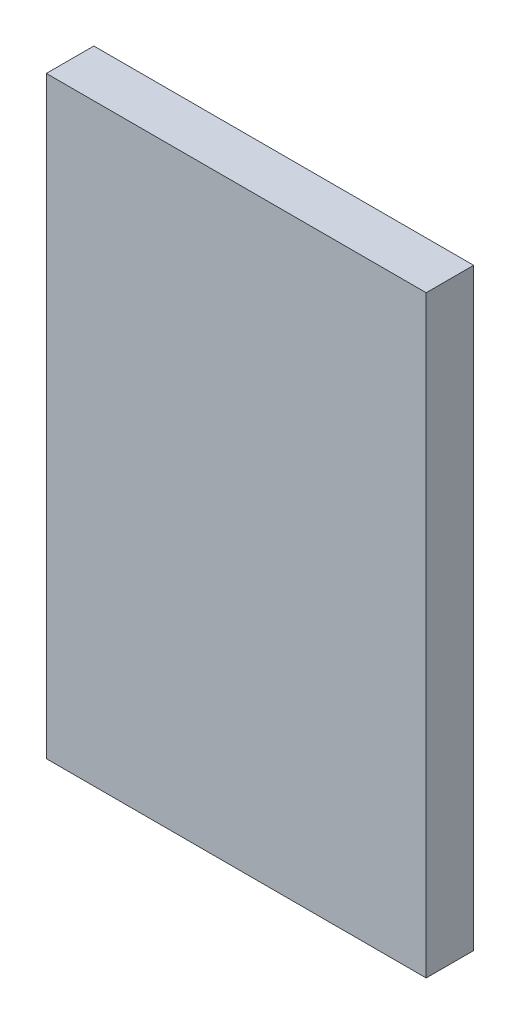
SolidWorks part; units mm, degrees
ref_plane "Alzado" through (0, 0, 0) normal (0, 0, 1) x (1, 0, 0)
ref_plane "Planta" through (0, 0, 0) normal (0, 1, 0) x (1, 0, 0)
ref_plane "Vista lateral" through (0, 0, 0) normal (1, 0, 0) x (0, 0, -1)
sketch "Croquis1" plane through (0, 0, 0) normal (0, 0, 1) x (1, 0, 0)
  line L1 (0, 0) -> (80, 0)
  line L2 (0, 0) -> (0, 125)
  line L3 (0, 125) -> (80, 125)
  line L4 (80, 0) -> (80, 125)
  dimension "D1" = 80
  dimension "D2" = 125
extrude "Saliente-Extruir1" add sketch "Croquis1" along normal blind 10
